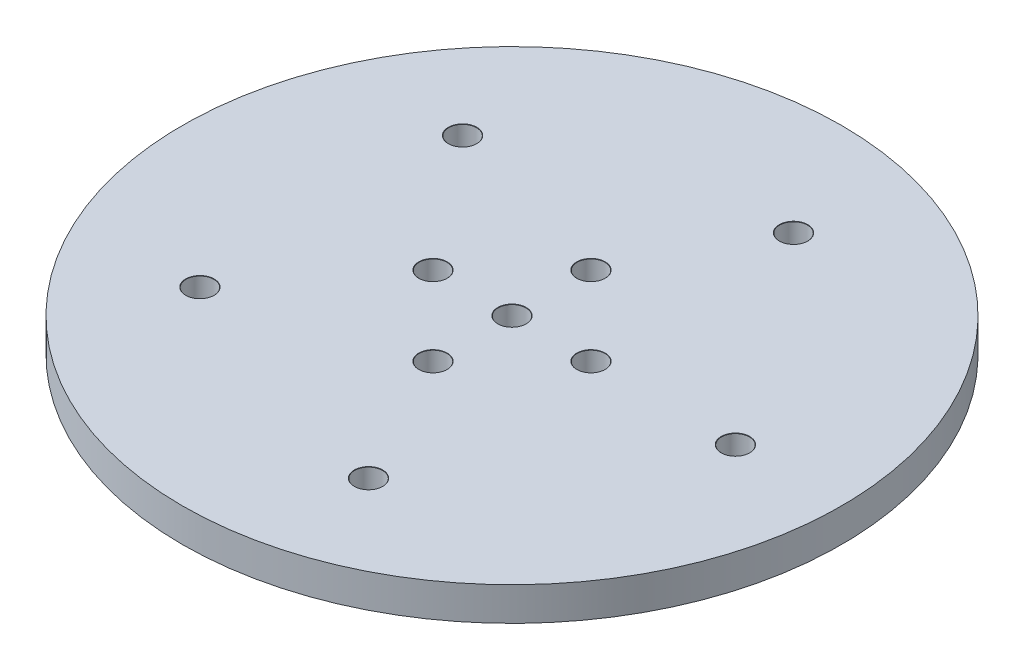
SolidWorks part; units mm, degrees
ref_plane "前视基准面" through (0, 0, 0) normal (0, 0, 1) x (1, 0, 0)
ref_plane "上视基准面" through (0, 0, 0) normal (0, 1, 0) x (1, 0, 0)
ref_plane "右视基准面" through (0, 0, 0) normal (1, 0, 0) x (0, 0, -1)
other "Configuration Table"
sketch "草图1" plane through (0, 0, 0) normal (0, 1, 0) x (1, 0, 0)
  circle A0 centre (0, 0) radius 29.5
  dimension "D1" = 59
extrude "凸台-拉伸1" add sketch "草图1" along normal blind 3
sketch "草图2" plane through (0, 3, 0) normal (0, 1, 0) x (1, 0, 0)
  line L0 (0, 0) -> (39.3262, 0) construction
  circle A0 centre (0, 0) radius 27.5 construction
  circle A1 centre (20, 0) radius 1.5
  circle A2 centre (6.1803, -19.0211) radius 1.5
  circle A3 centre (-16.1803, -11.7557) radius 1.5
  circle A4 centre (-16.1803, 11.7557) radius 1.5
  circle A5 centre (6.1803, 19.0211) radius 1.5
  point P3 (20, 0)
  point P9 (6.1803, -19.0211)
  point P11 (-16.1803, -11.7557)
  point P13 (-16.1803, 11.7557)
  point P15 (6.1803, 19.0211)
  point P17 (0, 0)
  dimension "D1" = 55
  dimension "D3" = 5
  dimension "D4" = 3
  dimension "D2" = 20
hole_wizard "M3 螺纹孔的螺纹孔钻头1" positions "草图2" profile "草图4" hole size "M3" standard "GB"
sketch "草图4" plane through (6.1803, 3, -19.0211) normal (1, 0, 0) x (0, 0, 1)
  line L0 (0, 0) -> (0, 3)
  line L1 (0, 3) -> (1.25, 3)
  line L2 (1.25, 3) -> (1.25, 0.025)
  line L3 (1.25, 0.025) -> (1.275, 0)
  line L5 (1.275, 0) -> (0, 0)
  line L6 (-1.25, 0.025) -> (-1.275, 0) construction
  line L11 (0, -6.35) -> (0, 107.95) construction
  dimension "通孔孔直径" = 2.5
  dimension "通孔孔深度" = 3
  dimension "近端锥形沉头孔直径" = 2.55
  dimension "近端锥形沉头孔角度" = 90
cosmetic thread "装饰螺纹线1" parameters "D2"=3
cosmetic thread "装饰螺纹线2" parameters "D2"=3
cosmetic thread "装饰螺纹线3" parameters "D2"=3
cosmetic thread "装饰螺纹线4" parameters "D2"=3
cosmetic thread "装饰螺纹线5" parameters "D2"=3
sketch "草图5" plane through (0, 3, 0) normal (0, 1, 0) x (1, 0, 0)
  line L0 (0, 0) -> (15.2665, 0) construction
  circle A0 centre (0, 0) radius 9.9
  point P3 (7.0711, 0)
  point P8 (0, -7.0711)
  point P9 (-7.0711, 0)
  point P10 (0, 7.0711)
  point P11 (0, 0)
  dimension "D1" = 19.8
  dimension "D3" = 10
  dimension "D2" = 4
hole_wizard "M3 螺纹孔的螺纹孔钻头2" positions "草图5" profile "草图6" hole size "M3" standard "GB" end condition through all
sketch "草图6" plane through (0, 3, 0) normal (1, 0, 0) x (0, 0, 1)
  line L0 (0, 0) -> (0, 3)
  line L1 (0, 3) -> (1.25, 3)
  line L2 (1.25, 3) -> (1.25, 0.025)
  line L3 (1.25, 0.025) -> (1.275, 0)
  line L5 (1.275, 0) -> (0, 0)
  line L6 (-1.25, 0.025) -> (-1.275, 0) construction
  line L11 (0, -6.35) -> (0, 107.95) construction
  dimension "通孔孔直径" = 2.5
  dimension "通孔孔深度" = 3
  dimension "近端锥形沉头孔直径" = 2.55
  dimension "近端锥形沉头孔角度" = 90
